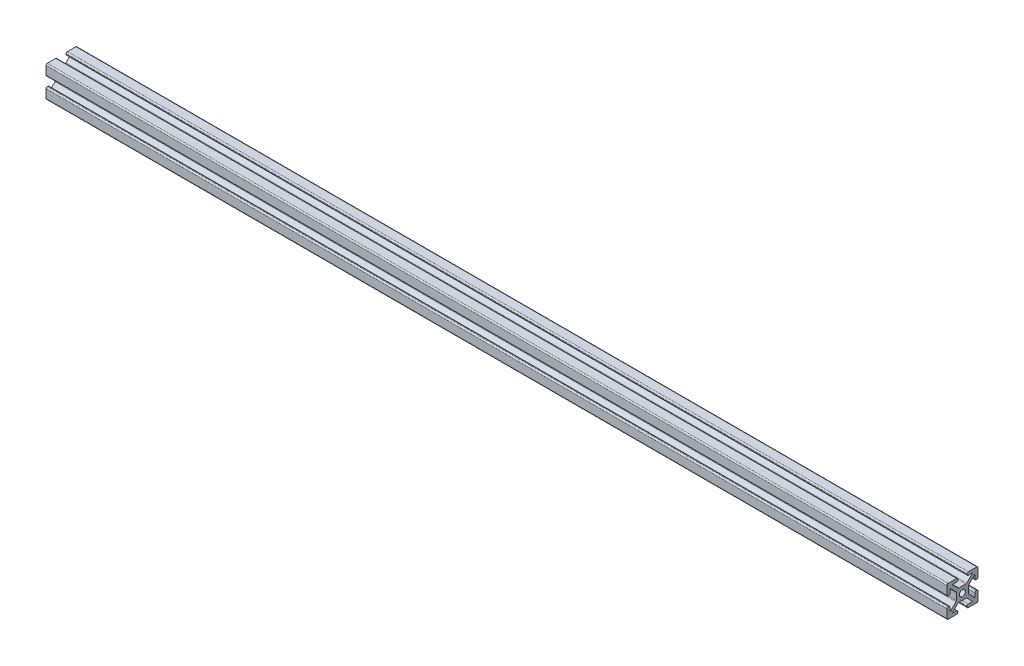
SolidWorks part; units mm, degrees
material "1060 Alloy"
ref_plane "Front Plane" through (0, 0, 0) normal (0, 0, 1) x (1, 0, 0)
ref_plane "Top Plane" through (0, 0, 0) normal (0, 1, 0) x (1, 0, 0)
ref_plane "Right Plane" through (0, 0, 0) normal (1, 0, 0) x (0, 0, -1)
sketch "Sketch2" plane through (0, 0, 0) normal (0, 0, 1) x (1, 0, 0)
  line L0 (-256.36, 0) -> (323.64, 0)
  dimension "D1" = 580
other "Profile 4X4(1)"
ref_plane "Plane1" through (-256.36, 0, 0) normal (1, 0, 0) x (0, 1, 0)
sketch "Sketch1" plane through (-256.36, 0, 0) normal (1, 0, 0) x (0, 1, 0)
  line L0 (-3, 9.2) -> (-3, 8.8)
  line L1 (-2.2544, 4) -> (2.2544, 4)
  line L2 (-4, 2.2544) -> (-4, -2.2544)
  line L3 (-2.2544, -4) -> (2.2544, -4)
  line L4 (4, 2.2544) -> (4, -2.2544)
  line L7 (-6.5858, 8) -> (-3.8, 8)
  line L8 (-8, 6.5858) -> (-8, 3.8)
  line L9 (-6.5858, -8) -> (-3.8, -8)
  line L10 (8, 6.5858) -> (8, 3.8)
  line L12 (9.7657, -9.7657) -> (10, -10) construction
  line L13 (-9.2, 10) -> (-3.8, 10)
  line L14 (-10, 9.2) -> (-10, 3.8)
  line L15 (-9.2, -10) -> (-3.8, -10)
  line L16 (10, 9.2) -> (10, 3.8)
  line L17 (-10, 10) -> (-9.7657, 9.7657) construction
  line L18 (-10, -10) -> (-9.7657, -9.7657) construction
  line L21 (3, 9.2) -> (3, 8.8)
  line L22 (3, -9.2) -> (3, -8.8)
  line L23 (-3, -9.2) -> (-3, -8.8)
  line L24 (3.8, 10) -> (9.2, 10)
  line L25 (3.8, 8) -> (6.5858, 8)
  line L26 (-9.2, 3) -> (-8.8, 3)
  line L27 (9.2, 3) -> (8.8, 3)
  line L28 (9.2, -3) -> (8.8, -3)
  line L29 (-9.2, -3) -> (-8.8, -3)
  line L30 (-10, -3.8) -> (-10, -9.2)
  line L31 (-8, -3.8) -> (-8, -6.5858)
  line L32 (8, -3.8) -> (8, -6.5858)
  line L33 (10, -3.8) -> (10, -9.2)
  line L34 (3.8, -8) -> (6.5858, -8)
  line L35 (3.8, -10) -> (9.2, -10)
  line L36 (6.5858, 8) -> (2.8201, 4.2343)
  line L37 (8, 6.5858) -> (4.2343, 2.8201)
  line L38 (8, -6.5858) -> (4.2343, -2.8201)
  line L39 (6.5858, -8) -> (2.8201, -4.2343)
  line L40 (-6.5858, -8) -> (-2.8201, -4.2343)
  line L41 (-8, -6.5858) -> (-4.2343, -2.8201)
  line L42 (-8, 6.5858) -> (-4.2343, 2.8201)
  line L43 (-6.5858, 8) -> (-2.8201, 4.2343)
  line L47 (9.7657, 9.7657) -> (10, 10) construction
  circle A0 centre (0, 0) radius 2
  arc A1 (9.2, -3) -> (10, -3.8) centre (9.2, -3.8) cw
  arc A2 (8.8, -3) -> (8, -3.8) centre (8.8, -3.8) ccw
  arc A3 (3, -9.2) -> (3.8, -10) centre (3.8, -9.2) ccw
  arc A4 (3, -8.8) -> (3.8, -8) centre (3.8, -8.8) cw
  arc A5 (-3, -9.2) -> (-3.8, -10) centre (-3.8, -9.2) cw
  arc A6 (-3, -8.8) -> (-3.8, -8) centre (-3.8, -8.8) ccw
  arc A7 (-8.8, -3) -> (-8, -3.8) centre (-8.8, -3.8) cw
  arc A8 (-9.2, -3) -> (-10, -3.8) centre (-9.2, -3.8) ccw
  arc A9 (-10, -9.2) -> (-9.2, -10) centre (-9.2, -9.2) ccw
  arc A10 (9.2, -10) -> (10, -9.2) centre (9.2, -9.2) ccw
  arc A11 (9.2, 10) -> (10, 9.2) centre (9.2, 9.2) cw
  arc A12 (-9.2, 10) -> (-10, 9.2) centre (-9.2, 9.2) ccw
  arc A13 (9.2, 3) -> (10, 3.8) centre (9.2, 3.8) ccw
  arc A14 (8.8, 3) -> (8, 3.8) centre (8.8, 3.8) cw
  arc A15 (3, 9.2) -> (3.8, 10) centre (3.8, 9.2) cw
  arc A16 (3, 8.8) -> (3.8, 8) centre (3.8, 8.8) ccw
  arc A17 (-3, 9.2) -> (-3.8, 10) centre (-3.8, 9.2) ccw
  arc A18 (-3, 8.8) -> (-3.8, 8) centre (-3.8, 8.8) cw
  arc A19 (-8.8, 3) -> (-8, 3.8) centre (-8.8, 3.8) ccw
  arc A20 (-9.2, 3) -> (-10, 3.8) centre (-9.2, 3.8) cw
  arc A21 (-2.8201, 4.2343) -> (-2.2544, 4) centre (-2.2544, 4.8) ccw
  arc A22 (4.2343, 2.8201) -> (4, 2.2544) centre (4.8, 2.2544) ccw
  arc A23 (2.8201, 4.2343) -> (2.2544, 4) centre (2.2544, 4.8) cw
  arc A24 (4.2343, -2.8201) -> (4, -2.2544) centre (4.8, -2.2544) cw
  arc A25 (2.8201, -4.2343) -> (2.2544, -4) centre (2.2544, -4.8) ccw
  arc A26 (-2.8201, -4.2343) -> (-2.2544, -4) centre (-2.2544, -4.8) cw
  arc A27 (-4.2343, -2.8201) -> (-4, -2.2544) centre (-4.8, -2.2544) ccw
  arc A28 (-4.2343, 2.8201) -> (-4, 2.2544) centre (-4.8, 2.2544) cw
  point P7 (0, 0)
  point P10 (-2.5858, 4)
  point P53 (10, -3)
  point P56 (8, -3)
  point P59 (3, -10)
  point P62 (3, -8)
  point P65 (-3, -10)
  point P68 (-3, -8)
  point P71 (-8, -3)
  point P74 (-10, -3)
  point P89 (10, 3)
  point P92 (8, 3)
  point P95 (3, 10)
  point P98 (3, 8)
  point P101 (-3, 10)
  point P104 (-3, 8)
  point P107 (-8, 3)
  point P110 (-10, 3)
  point P116 (4, 2.5858)
  point P119 (2.5858, 4)
  point P122 (4, -2.5858)
  point P125 (2.5858, -4)
  point P128 (-2.5858, -4)
  point P131 (-4, -2.5858)
  point P134 (-4, 2.5858)
  dimension "D3" = 4
  dimension "D11" = 0.8
  dimension "D12" = 0.8
  dimension "D2" = 0.8
  dimension "D4" = 20
  dimension "D6" = 20
  dimension "D8" = 7
  dimension "D9" = 7
